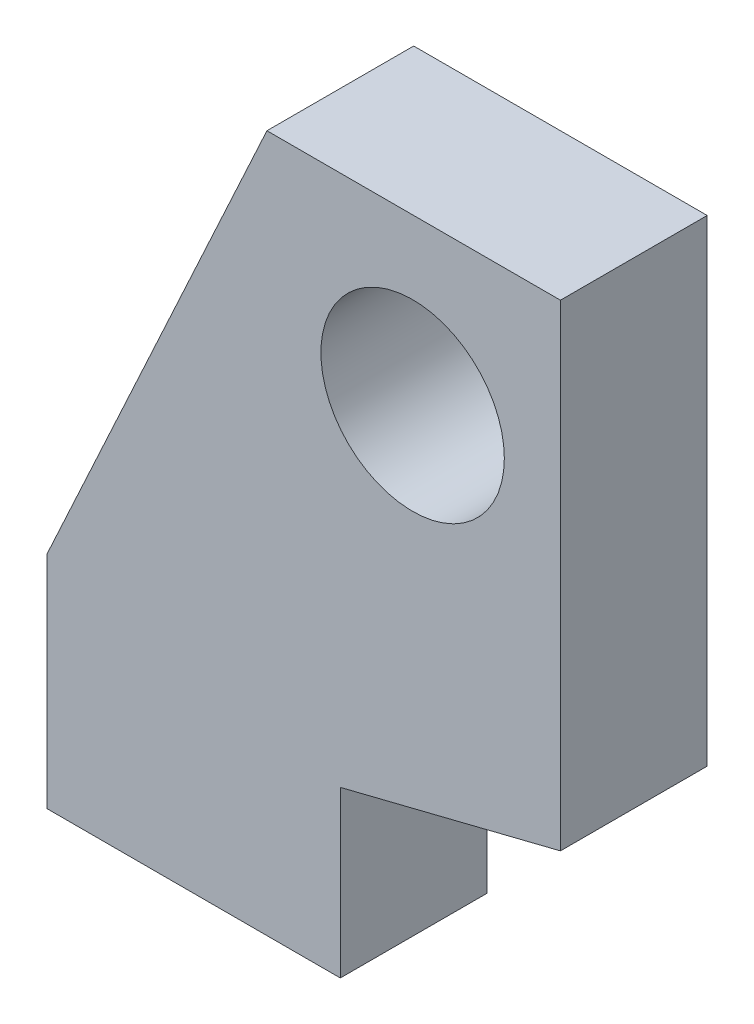
SolidWorks part; units mm, degrees
ref_plane "Front Plane" through (0, 0, 0) normal (0, 0, 1) x (1, 0, 0)
ref_plane "Top Plane" through (0, 0, 0) normal (0, 1, 0) x (1, 0, 0)
ref_plane "Right Plane" through (0, 0, 0) normal (1, 0, 0) x (0, 0, -1)
sketch "Sketch1" plane through (0, 0, 0) normal (0, 0, 1) x (1, 0, 0)
  line L0 (0, -2) -> (8, 0)
  line L1 (0, 0) -> (8, 0)
  line L2 (0, 0) -> (0, 13)
  line L3 (0, 13) -> (8, 13)
  line L4 (8, 0) -> (8, 13)
  line L5 (0, 0) -> (-6, 0)
  line L6 (0, 0) -> (0, -2)
  line L7 (0, -2) -> (-6, -2)
  line L8 (-6, 0) -> (-6, -2)
  line L13 (-6, -2) -> (0, -2)
  line L14 (-6, -2) -> (-6, -6)
  line L15 (-6, -6) -> (0, -6)
  line L16 (0, -2) -> (0, -6)
  line L17 (-6, 0) -> (0, 13)
  line L18 (0, -6) -> (2, -6)
  line L19 (0, -6) -> (0, 0)
  line L20 (0, 0) -> (2, 0)
  line L21 (2, -6) -> (2, 0)
  circle A0 centre (3.9708, 8.5) radius 2.5
  dimension "D3" = 5
  dimension "D1" = 8
  dimension "D2" = 13
  dimension "D4" = 4.5
  dimension "D5" = 6
  dimension "D6" = 2
  dimension "D7" = 4
  dimension "D8" = 2
extrude "Boss-Extrude1" add sketch "Sketch1" along normal blind 4
